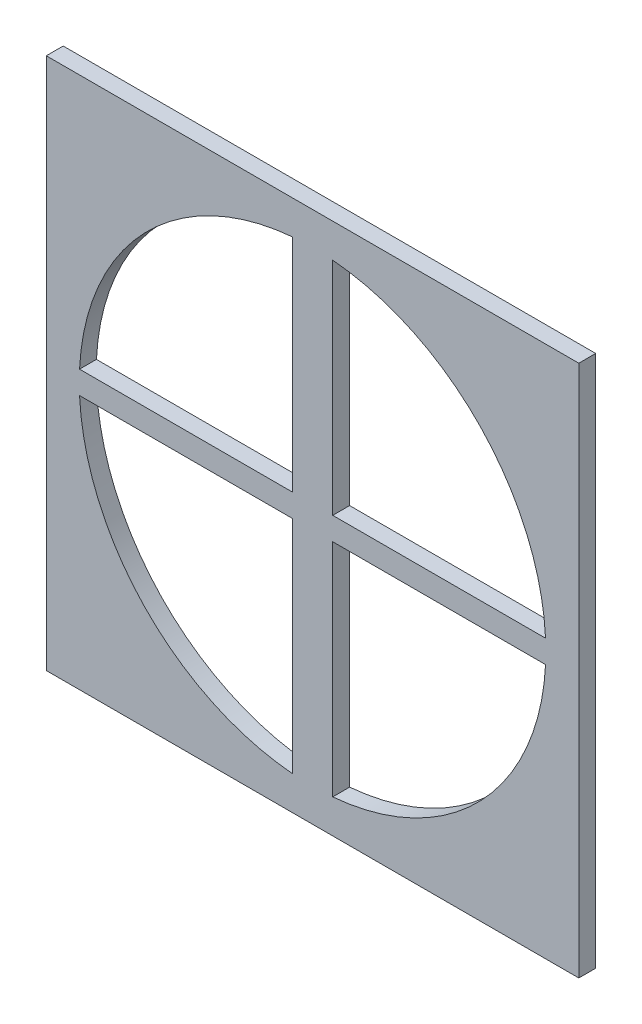
SolidWorks part; units mm, degrees
ref_plane "Front Plane" through (0, 0, 0) normal (0, 0, 1) x (1, 0, 0)
ref_plane "Top Plane" through (0, 0, 0) normal (0, 1, 0) x (1, 0, 0)
ref_plane "Right Plane" through (0, 0, 0) normal (1, 0, 0) x (0, 0, -1)
sketch "Sketch1" plane through (0, 0, 0) normal (0, 0, 1) x (1, 0, 0)
  line L1 (-40.005, -40.0005) -> (40.005, -40.0005)
  line L2 (-40.005, -40.0005) -> (-40.005, 40.0005)
  line L3 (-40.005, 40.0005) -> (40.005, 40.0005)
  line L4 (40.005, -40.0005) -> (40.005, 40.0005)
  line L5 (-40.005, -40.0005) -> (40.005, 40.0005) construction
  line L6 (-40.005, 40.0005) -> (40.005, -40.0005) construction
  point P0 (0, 0)
  dimension "D1" = 80.01
  dimension "D2" = 80.001
extrude "Boss-Extrude1" add sketch "Sketch1" along normal blind 5.08
sketch "Sketch2" plane through (0, 0, 5.08) normal (0, 0, 1) x (1, 0, 0)
  line L0 (-40.005, 40.0005) -> (40.005, -40.0005) construction
  line L1 (40.005, -40.0005) -> (40.005, 40.0005) construction
  line L2 (40.005, 40.0005) -> (-40.005, -40.0005) construction
  circle A0 centre (0, 0) radius 35.052
  dimension "D1" = 70.104
extrude "Cut-Extrude1" cut sketch "Sketch2" against normal blind 5.08
sketch "Sketch3" plane through (0, 0, 5.08) normal (0, 0, 1) x (1, 0, 0)
  line L0 (0, 40.0005) -> (0, -40.0005)
  line L1 (40.005, 40.0005) -> (-40.005, 40.0005) construction
  line L2 (-40.005, -40.0005) -> (40.005, -40.0005) construction
  line L3 (40.005, -40.0005) -> (40.005, 40.0005) construction
  line L4 (-3.0327, -40.0005) -> (3.0327, -40.0005)
  line L5 (-3.0327, -40.0005) -> (-3.0327, 40.0005)
  line L6 (-3.0327, 40.0005) -> (3.0327, 40.0005)
  line L7 (3.0327, -40.0005) -> (3.0327, 40.0005)
  line L8 (-3.0327, -40.0005) -> (3.0327, 40.0005) construction
  line L9 (-3.0327, 40.0005) -> (3.0327, -40.0005) construction
  line L10 (-40.005, -1.7166) -> (40.005, -1.7166)
  line L11 (-40.005, -1.7166) -> (-40.005, 1.7166)
  line L12 (-40.005, 1.7166) -> (40.005, 1.7166)
  line L13 (40.005, -1.7166) -> (40.005, 1.7166)
  line L14 (-40.005, -1.7166) -> (40.005, 1.7166) construction
  line L15 (-40.005, 1.7166) -> (40.005, -1.7166) construction
  point P6 (0, 0)
  point P11 (0, 0)
  circle M1 centre (0, 0) radius 35.052
extrude "Boss-Extrude3" add sketch "Sketch3" against normal blind 5.08 contours L0 L12 L7 M1 | L5 L12 L0 M1 | L12 L10 L5 M1 | L12 L0 L10 L7 | L12 L5 L10 L0 | L10 L0 L7 M1 | L10 L5 L0 M1 | L12 L7 L10 M1
sketch "Sketch5" plane through (0, 0, 5.08) normal (0, 0, 1) x (1, 0, 0)
  line L1 (-59.1883, 52.6004) -> (76.4088, 52.6004)
  line L2 (-59.1883, 52.6004) -> (-59.1883, -53.9556)
  line L3 (-59.1883, -53.9556) -> (76.4088, -53.9556)
  line L4 (76.4088, 52.6004) -> (76.4088, -53.9556)
extrude "Cut-Extrude2" cut sketch "Sketch5" against normal blind 2.54
